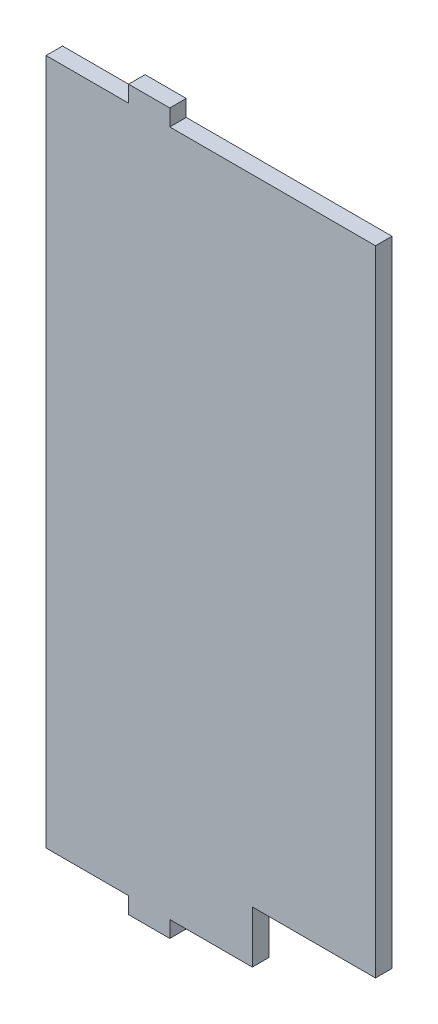
SolidWorks part; units mm, degrees
ref_plane "Plan de face" through (0, 0, 0) normal (0, 0, 1) x (1, 0, 0)
ref_plane "Plan de dessus" through (0, 0, 0) normal (0, 1, 0) x (1, 0, 0)
ref_plane "Plan de droite" through (0, 0, 0) normal (1, 0, 0) x (0, 0, -1)
sketch "Esquisse1" plane through (0, 0, 0) normal (0, 0, 1) x (1, 0, 0)
  line L0 (184.3802, 0) -> (-369.1376, 0) construction
  line L1 (-197.9203, 125) -> (-77.9203, 125)
  line L2 (-197.9203, 125) -> (-197.9203, -125)
  line L3 (-197.9203, -125) -> (-77.9203, -125)
  line L4 (-77.9203, 125) -> (-77.9203, -125)
  dimension "D1" = 250
  dimension "D2" = 120
  dimension "D3" = 125
extrude "Boss.-Extru.1" add sketch "Esquisse1" along normal blind 6
sketch "Esquisse2" plane through (0, 0, 6) normal (0, 0, 1) x (1, 0, 0)
  line L0 (-197.9203, -125) -> (-77.9203, -125) construction
  line L1 (-167.8503, -125) -> (-152.8503, -125)
  line L2 (-167.8503, -125) -> (-167.8503, -131)
  line L3 (-167.8503, -131) -> (-152.8503, -131)
  line L4 (-152.8503, -125) -> (-152.8503, -131)
  line L5 (-197.9203, 125) -> (-197.9203, -125) construction
  line L6 (50.1793, 0) -> (-261.8778, 0) construction
  line L7 (-152.8503, 125) -> (-152.8503, 131)
  line L8 (-167.8503, 131) -> (-152.8503, 131)
  line L9 (-167.8503, 125) -> (-167.8503, 131)
  line L10 (-167.8503, 125) -> (-152.8503, 125)
  dimension "D1" = 15
  dimension "D2" = 6
  dimension "D3" = 30.07
extrude "Boss.-Extru.3" add sketch "Esquisse2" against normal blind 6
sketch "Esquisse3" plane through (0, 0, 6) normal (0, 0, 1) x (1, 0, 0)
  line L1 (-77.9203, -125) -> (-122.7803, -125)
  line L2 (-77.9203, -125) -> (-77.9203, -106)
  line L3 (-77.9203, -106) -> (-122.7803, -106)
  line L4 (-122.7803, -125) -> (-122.7803, -106)
  dimension "D1" = 44.86
  dimension "D2" = 19
extrude "Enlèv. mat.-Extru.1" cut sketch "Esquisse3" against normal blind 6
equation "\"D3@Esquisse1\"=\"D1@Esquisse1\"/2"
